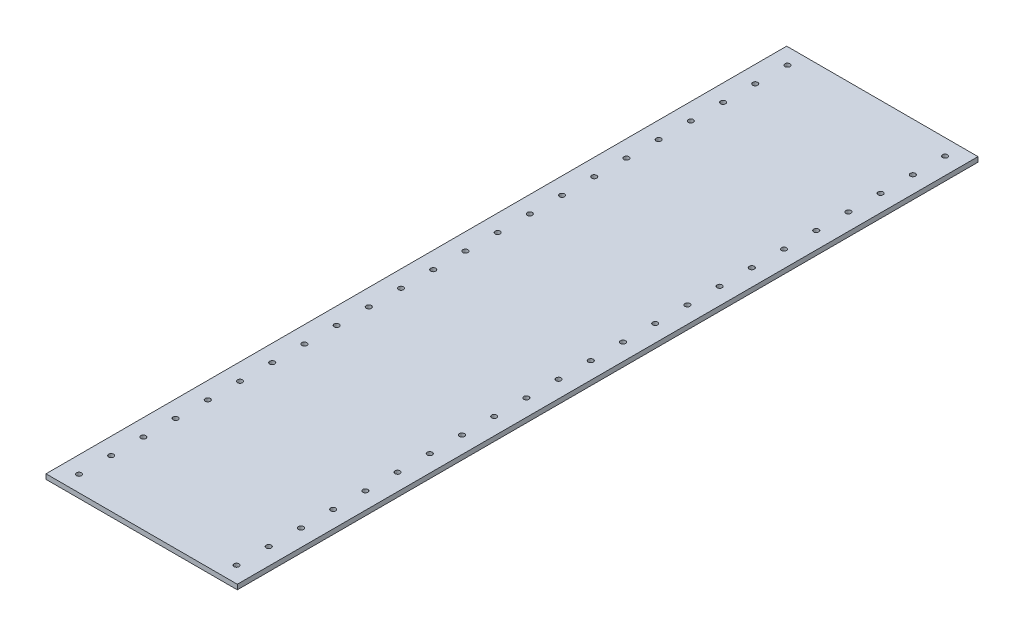
SolidWorks part; units mm, degrees
ref_plane "Front" through (0, 0, 0) normal (0, 0, 1) x (1, 0, 0)
ref_plane "Top" through (0, 0, 0) normal (0, 1, 0) x (1, 0, 0)
ref_plane "Right" through (0, 0, 0) normal (1, 0, 0) x (0, 0, -1)
sketch "Sketch1" plane through (0, 0, 0) normal (0, 1, 0) x (1, 0, 0)
  line L1 (-62.38, -241.5) -> (62.38, -241.5)
  line L2 (-62.38, -241.5) -> (-62.38, 241.5)
  line L3 (-62.38, 241.5) -> (62.38, 241.5)
  line L4 (62.38, -241.5) -> (62.38, 241.5)
  line L5 (-62.38, -241.5) -> (62.38, 241.5) construction
  line L6 (-62.38, 241.5) -> (62.38, -241.5) construction
  point P0 (0, 0)
  dimension "D1" = 483
  dimension "D2" = 124.76
extrude "Boss-Extrude1" add sketch "Sketch1" along normal blind 3.175
hole_wizard "Tap Drill for M4x0.7 Tap1" positions "Sketch2" profile "Sketch3" hole size "M4x0.7" standard "ANSI Metric" end condition through all
sketch "Sketch2" plane through (0, 3.175, 0) normal (0, 1, 0) x (1, 0, 0)
  line L0 (-62.38, 241.5) -> (-62.38, -241.5) construction
  line L1 (-62.38, -241.5) -> (62.38, -241.5) construction
  point P0 (-51.38, -231)
  point P18 (-51.38, -210)
  point P19 (-51.38, -189)
  point P20 (-51.38, -168)
  point P21 (-51.38, -147)
  point P22 (-51.38, -126)
  point P23 (-51.38, -105)
  point P24 (-51.38, -84)
  point P25 (-51.38, -63)
  point P26 (-51.38, -42)
  point P27 (-51.38, -21)
  point P28 (-51.38, 0)
  point P29 (-51.38, 21)
  point P30 (-51.38, 42)
  point P31 (-51.38, 63)
  point P32 (-51.38, 84)
  point P33 (-51.38, 105)
  point P34 (-51.38, 126)
  point P35 (-51.38, 147)
  point P36 (-51.38, 168)
  point P37 (-51.38, 189)
  point P38 (-51.38, 210)
  point P39 (-51.38, 231)
  point P41 (51.38, -210)
  point P42 (51.38, -189)
  point P43 (51.38, -168)
  point P44 (51.38, -147)
  point P45 (51.38, -126)
  point P46 (51.38, -105)
  point P47 (51.38, -84)
  point P48 (51.38, -63)
  point P49 (51.38, -42)
  point P50 (51.38, -21)
  point P51 (51.38, 0)
  point P52 (51.38, 21)
  point P53 (51.38, 42)
  point P54 (51.38, 63)
  point P55 (51.38, 84)
  point P56 (51.38, 105)
  point P57 (51.38, 126)
  point P58 (51.38, 147)
  point P59 (51.38, 168)
  point P60 (51.38, 189)
  point P61 (51.38, 210)
  point P62 (51.38, 231)
  point P64 (51.38, -231)
  dimension "D1" = 11
  dimension "D2" = 10.5
  dimension "D5" = 21
  dimension "D6" = 102.76
  dimension "D3" = 23
  dimension "D4" = 2
sketch "Sketch3" plane through (-51.38, 3.175, 231) normal (1, 0, 0) x (0, 0, 1)
  line L0 (0, 0) -> (0, 3.175)
  line L1 (0, 3.175) -> (1.65, 3.175)
  line L2 (1.65, 3.175) -> (1.65, 0)
  line L5 (1.65, 0) -> (0, 0)
  line L11 (0, -6.35) -> (0, 107.95) construction
  dimension "Thru Hole Dia." = 3.3
  dimension "Thru Hole Depth" = 3.175
